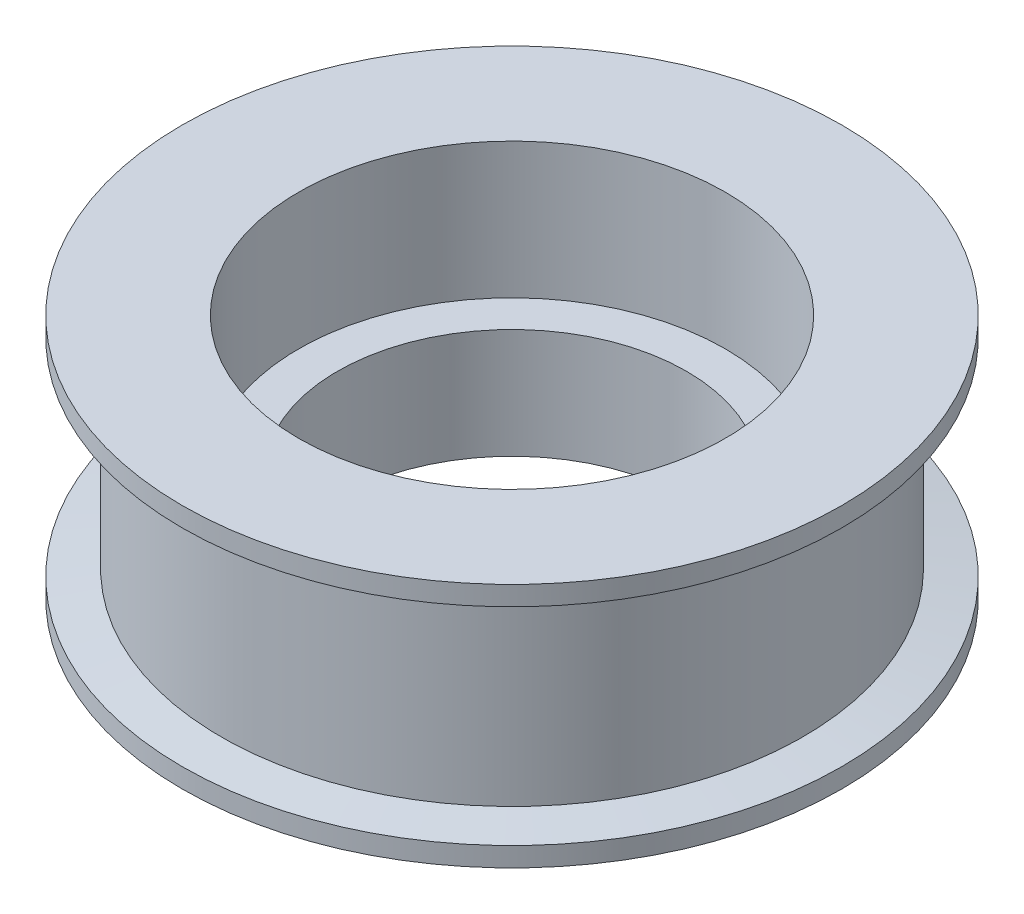
SolidWorks part; units mm, degrees
ref_plane "Front Plane" through (0, 0, 0) normal (0, 0, 1) x (1, 0, 0)
ref_plane "Top Plane" through (0, 0, 0) normal (0, 1, 0) x (1, 0, 0)
ref_plane "Right Plane" through (0, 0, 0) normal (1, 0, 0) x (0, 0, -1)
sketch "Sketch1" plane through (0, 0, 0) normal (0, 1, 0) x (1, 0, 0)
  circle A0 centre (0, 0) radius 11
  circle A1 centre (0, 0) radius 15
  dimension "D1" = 22
  dimension "D2" = 30
extrude "Boss-Extrude1" add sketch "Sketch1" along normal blind 11.66
sketch "Sketch2" plane through (0, 0, 0) normal (0, 0, 1) x (1, 0, 0)
  line L1 (15, 0) -> (15, 11.66) construction
  line L2 (15, 11.66) -> (17, 11.66)
  line L3 (15, 11.66) -> (15, 10.33)
  line L4 (15, 0.33) -> (17, 0)
  line L5 (17, 11.66) -> (17, 10.66)
  line L6 (15, 10.33) -> (17, 10.66)
  line L7 (15, -1) -> (17, -1)
  line L9 (0, 0) -> (0, 11.66) construction
  line L10 (17, -1) -> (17, 0)
  line L11 (11, 11.66) -> (-11, 11.66) construction
  line L13 (15, 0.33) -> (15, 4.66)
  line L14 (15, -1) -> (9, -1)
  line L15 (9, 0.33) -> (9, -1)
  line L16 (15, 4.66) -> (9, 4.66)
  line L17 (9, 0.33) -> (9, 4.66)
  dimension "D1" = 2
  dimension "D2" = 1.33
  dimension "D3" = 1.33
  dimension "D4" = 1
  dimension "D5" = 1
  dimension "D6" = 10
  dimension "D7" = 8
  dimension "D8" = 6
  dimension "D9" = 7
  dimension "D10" = 5.66
revolve "Revolve1" add sketch "Sketch2" angle 360 about L9
